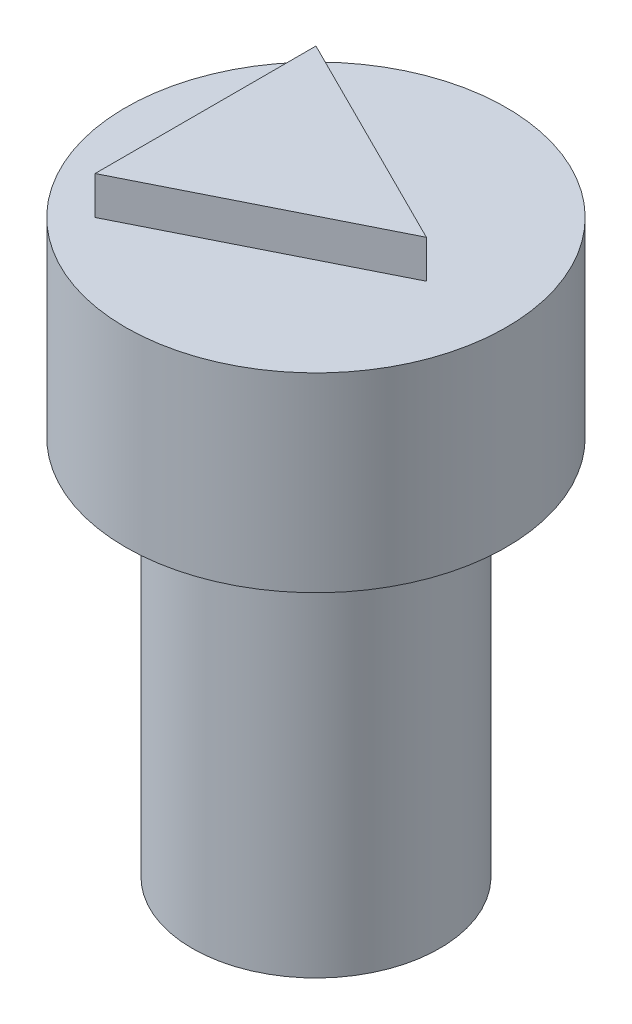
SolidWorks part; units mm, degrees
ref_plane "Front Plane" through (0, 0, 0) normal (0, 0, 1) x (1, 0, 0)
ref_plane "Top Plane" through (0, 0, 0) normal (0, 1, 0) x (1, 0, 0)
ref_plane "Right Plane" through (0, 0, 0) normal (1, 0, 0) x (0, 0, -1)
sketch "Sketch1" plane through (0, 0, 0) normal (0, 1, 0) x (1, 0, 0)
  circle A0 centre (0, 0) radius 3.25
  dimension "D1" = 6.5
extrude "Boss-Extrude1" add sketch "Sketch1" along normal blind 10 contours A0
sketch "Sketch2" plane through (0, 0, 0) normal (0, -1, 0) x (1, 0, 0)
  circle A1 centre (0, 0) radius 1.75
  dimension "D1" = 3.5
extrude "Cut-Extrude1" cut sketch "Sketch2" against normal blind 2.5
sketch "Sketch6" plane through (0, 10, 0) normal (0, 1, 0) x (1, 0, 0)
  circle A0 centre (0, 0) radius 5
  dimension "D1" = 10
extrude "Boss-Extrude2" add sketch "Sketch6" along normal blind 5 contours A0
sketch "Sketch7" plane through (0, 15, 0) normal (0, 1, 0) x (1, 0, 0)
  line L0 (-2.9, 0) -> (2.9, 0) construction
  line L1 (-2.9, 2.9) -> (2.9, 2.9)
  line L2 (-2.9, 2.9) -> (-2.9, -2.9)
  line L3 (-2.9, -2.9) -> (2.9, -2.9)
  line L4 (2.9, 2.9) -> (2.9, -2.9)
  line L5 (-2.9, 2.9) -> (2.9, -2.9) construction
  line L6 (-2.9, -2.9) -> (2.9, 2.9) construction
  line L7 (-2.9, 2.9) -> (-2.9, -2.9)
  line L8 (-2.9, -2.9) -> (2.9, 0)
  line L9 (2.9, 0) -> (-2.9, 2.9)
  point P0 (0, 0)
  dimension "D1" = 5.8
  dimension "D2" = 5.8
sketch "Sketch9" plane through (0, 15, 0) normal (0, 1, 0) x (1, 0, 0)
  line L0 (-2.9, 2.9) -> (-2.9, -2.9)
  line L1 (-2.9, -2.9) -> (2.9, 0)
  line L2 (2.9, 0) -> (-2.9, 2.9)
extrude "Boss-Extrude3" add sketch "Sketch9" along normal blind 1
